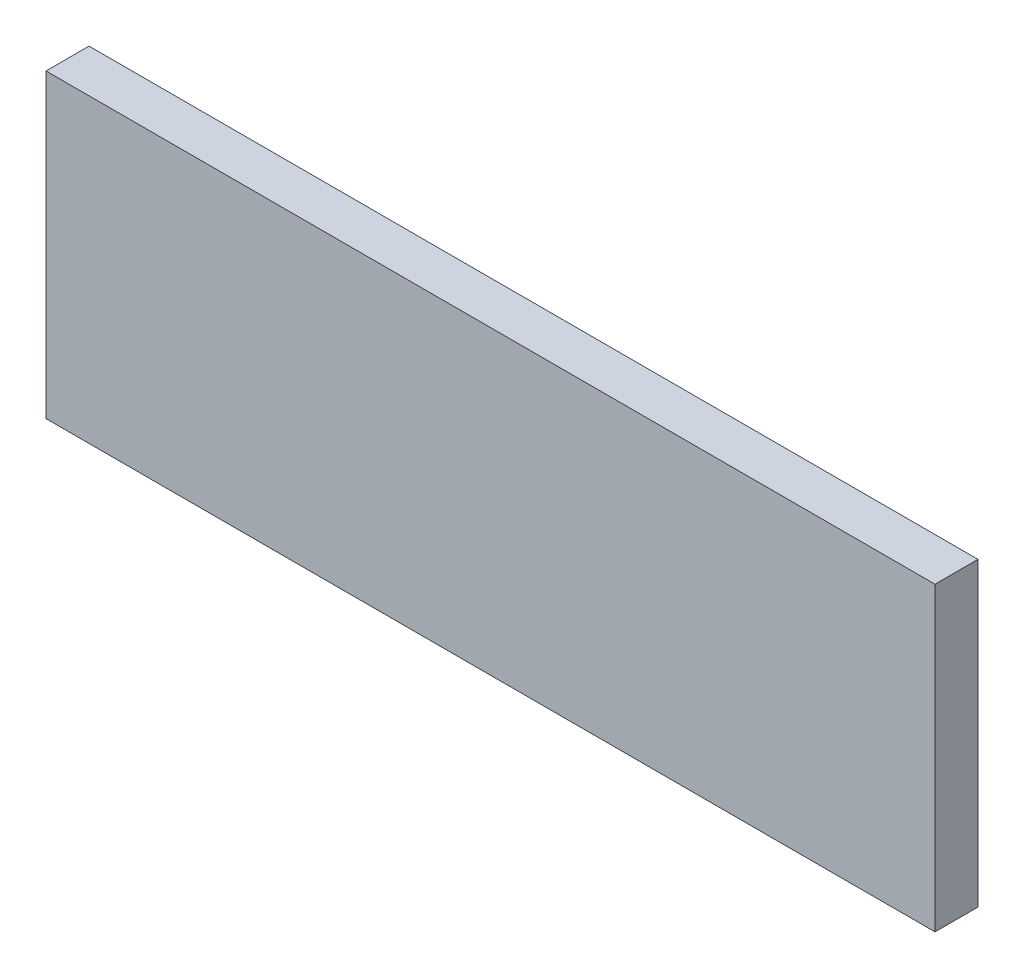
SolidWorks part; units mm, degrees
ref_plane "Plan de face" through (0, 0, 0) normal (0, 0, 1) x (1, 0, 0)
ref_plane "Plan de dessus" through (0, 0, 0) normal (0, 1, 0) x (1, 0, 0)
ref_plane "Plan de droite" through (0, 0, 0) normal (1, 0, 0) x (0, 0, -1)
sketch "Esquisse1" plane through (0, 0, 0) normal (0, 0, 1) x (1, 0, 0)
  line L0 (0, 5.25) -> (0, 0) construction
  line L1 (-15.5, 5.25) -> (15.5, 5.25)
  line L2 (-15.5, 5.25) -> (-15.5, -5.25)
  line L3 (-15.5, -5.25) -> (15.5, -5.25)
  line L4 (15.5, 5.25) -> (15.5, -5.25)
  line L5 (0, 0) -> (15.5, 0) construction
  dimension "D1" = 31
  dimension "D2" = 10.5
extrude "Boss.-Extru.1" add sketch "Esquisse1" along normal mid plane 1.5
